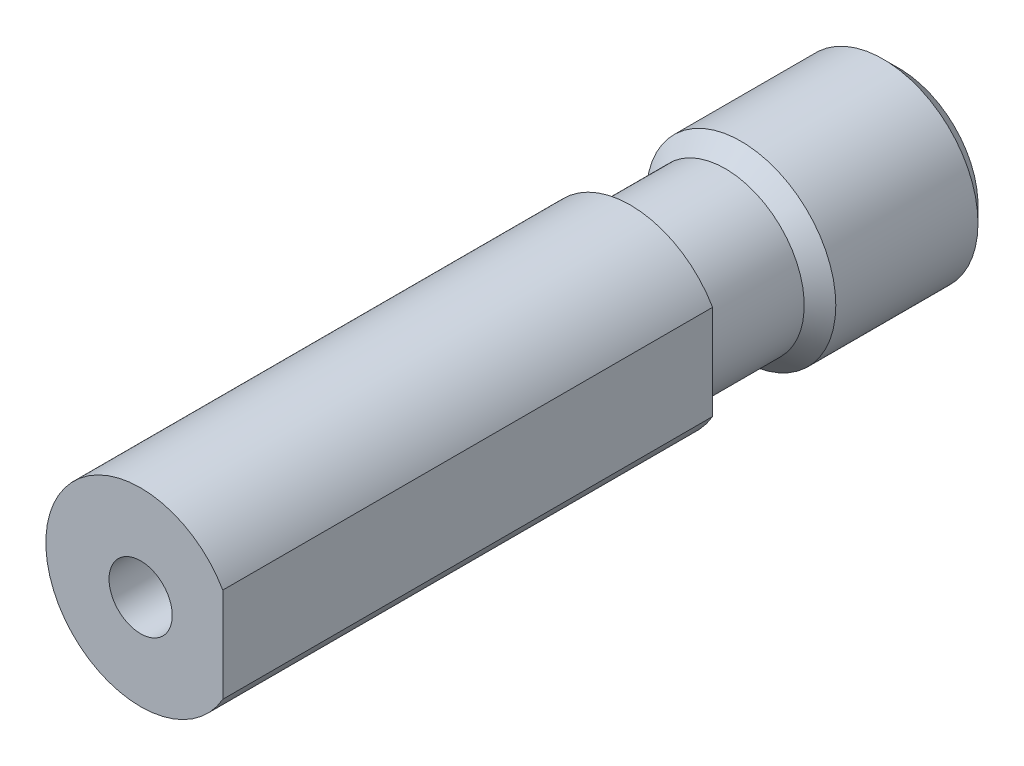
SolidWorks part; units mm, degrees
ref_plane "Front Plane" through (0, 0, 0) normal (0, 0, 1) x (1, 0, 0)
ref_plane "Top Plane" through (0, 0, 0) normal (0, 1, 0) x (1, 0, 0)
ref_plane "Right Plane" through (0, 0, 0) normal (1, 0, 0) x (0, 0, -1)
ref_plane "Plane1" through (0, 0, 8.5) normal (0, 0, -1) x (-1, 0, 0)
sketch "Sketch1" plane through (0, 0, 8.5) normal (0, 0, -1) x (-1, 0, 0)
  line L0 (-2.6, 1.4967) -> (-2.6, -1.4967)
  arc A0 (-2.6, -1.4967) -> (-2.6, 1.4967) centre (0, 0) ccw
extrude "Boss-Extrude1" add sketch "Sketch1" against normal blind 15.5
ref_plane "Plane2" through (0, 0, 0) normal (0, -1, 0) x (1, 0, 0)
sketch "Sketch2" plane through (0, 0, 0) normal (0, -1, 0) x (1, 0, 0)
  line L0 (2.5, 8.5) -> (0, 8.5)
  line L1 (0, 8.5) -> (0, 0)
  line L2 (0, 0) -> (3, 0)
  line L3 (3, 0) -> (3, 5)
  line L4 (3, 5) -> (2.5, 5.5)
  line L5 (2.5, 5.5) -> (2.5, 8.5)
  line L6 (0, 8.5) -> (0, 0) construction
revolve "Revolve1" add sketch "Sketch2" angle 360 about L6
hole_wizard "CBORE for #1 Binding Head Machine Screw1" positions "Sketch4" profile "Sketch3" counterbore size "#1" standard "ANSI Inch"
sketch "Sketch4" plane through (0, 0, 0) normal (0, 0, -1) x (-1, 0, 0)
  point P0 (0, 0)
sketch "Sketch3" plane through (0, 0, 0) normal (1, 0, 0) x (0, 1, 0)
  line L0 (0, 0) -> (0, 24)
  line L1 (0, 24) -> (1, 24)
  line L3 (1, 24) -> (1, 22)
  line L4 (1, 22) -> (2, 22)
  line L5 (2, 22) -> (2, 0)
  line L7 (2, 0) -> (0, 0)
  line L11 (0, -6.35) -> (0, 107.95) construction
  dimension "Thru Hole Dia." = 2
  dimension "Thru Hole Depth" = 24
  dimension "C'Bore Dia." = 4
  dimension "C'Bore Depth" = 22
chamfer "Chamfer1" distance 0.5 angle 45 1 edges at (-3, 0, 0)
